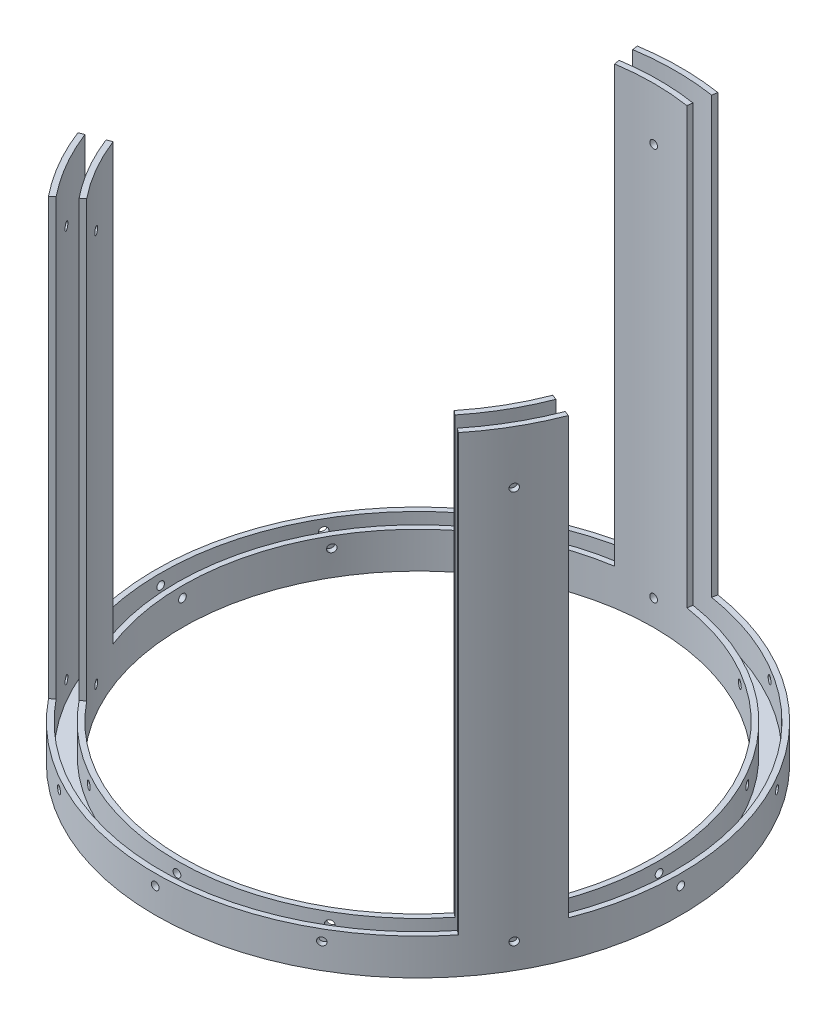
SolidWorks part; units mm, degrees
ref_plane "Front Plane" through (0, 0, 0) normal (0, 0, 1) x (1, 0, 0)
ref_plane "Top Plane" through (0, 0, 0) normal (0, 1, 0) x (1, 0, 0)
ref_plane "Right Plane" through (0, 0, 0) normal (1, 0, 0) x (0, 0, -1)
sketch "Sketch1" plane through (0, 0, 0) normal (0, 1, 0) x (1, 0, 0)
  circle A0 centre (0, 0) radius 92.075
  circle A1 centre (0, 0) radius 82.55
  dimension "D1" = 184.15
  dimension "D2" = 165.1
extrude "Boss-Extrude1" add sketch "Sketch1" along normal blind 12.7
sketch "Sketch3" plane through (0, 0, 0) normal (0, 0, 1) x (1, 0, 0)
  line L0 (92.075, 12.7) -> (-92.075, 12.7) construction
  circle A0 centre (0, 8.89) radius 1.3525
  dimension "D1" = 2.7051
  dimension "D2" = 3.81
extrude "Cut-Extrude2" cut sketch "Sketch3" against normal up to surface (92.0651 mm away)
pattern_circular "CirPattern1" count 12 over 360 about axis through (0, 12.7, 0) along (0, 1, 0) of "Cut-Extrude2"
sketch "Sketch4" plane through (0, 12.7, 0) normal (0, 1, 0) x (1, 0, 0)
  line L0 (-12.7, 81.5672) -> (-14.1654, 90.9788)
  line L1 (12.5999, 81.5827) -> (14.0538, 90.9961)
  line L2 (0, 0) -> (-12.7, 81.5672) construction
  arc A0 (-14.1654, 90.9788) -> (14.0538, 90.9961) centre (0, 0) cw
  circle A1 centre (0, 0) radius 92.075 construction
  arc A2 (-12.7, 81.5672) -> (12.5999, 81.5827) centre (0, 0) cw
  circle A4 centre (0, 0) radius 82.55 construction
  point P8 (0, 0)
  dimension "D2" = 25.4
  dimension "D1" = 12.7
extrude "Boss-Extrude2" add sketch "Sketch4" along normal blind 152.4
pattern_linear "LPattern1" count 2 spacing 137.668 along (0, 1, 0) of "Cut-Extrude2"
pattern_circular "CirPattern2" count 3 over 360 about axis through (0, 0, 0) along (0, 1, 0) of "LPattern1", "Boss-Extrude2"
sketch "Sketch2" plane through (0, 12.7, 0) normal (0, 1, 0) x (1, 0, 0)
  circle A0 centre (0, 0) radius 84.455
  circle A1 centre (0, 0) radius 90.17
  dimension "D1" = 180.34
  dimension "D2" = 168.91
extrude "Cut-Extrude1" cut sketch "Sketch2" against normal blind 10.16 and the other way up to surface other way up to face at (-0.0532, 165.1, -86.7969)
